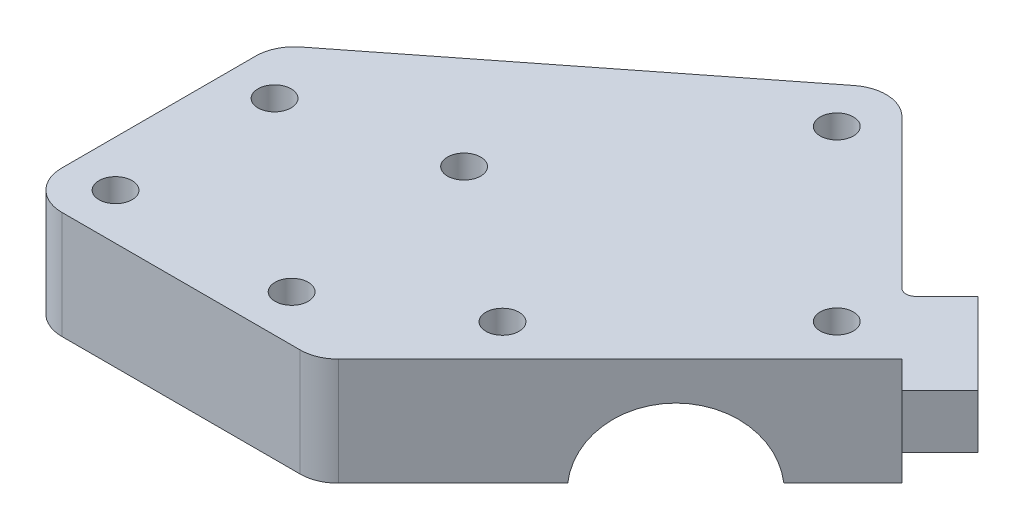
SolidWorks part; units mm, degrees
ref_plane "前视基准面" through (0, 0, 0) normal (0, 0, 1) x (1, 0, 0)
ref_plane "上视基准面" through (0, 0, 0) normal (0, 1, 0) x (1, 0, 0)
ref_plane "右视基准面" through (0, 0, 0) normal (1, 0, 0) x (0, 0, -1)
ref_plane "基准面4" through (0, 1, 0) normal (0, -1, 0) x (1, 0, 0)
sketch "草图1" plane through (0, 1, 0) normal (0, -1, 0) x (1, 0, 0)
  line L0 (4.7435, -52.275) -> (35.2198, -21.7987)
  line L1 (35.2198, -21.7987) -> (-2.9289, 16.35)
  line L2 (-2.9289, 16.35) -> (-41.0289, 16.35)
  line L3 (-41.0289, 16.35) -> (-41.0289, -16.35)
  line L4 (-41.0289, -16.35) -> (4.7435, -52.275)
extrude "凸台-拉伸1" add sketch "草图1" against normal blind 14
ref_plane "基准面5" through (0, 15, 0) normal (0, 1, 0) x (1, 0, 0)
sketch "草图2" plane through (0, 15, 0) normal (0, 1, 0) x (1, 0, 0)
  line L0 (35.2198, 21.7987) -> (38.7553, 18.2632)
  line L1 (38.7553, 18.2632) -> (43.705, 23.2129)
  line L2 (43.705, 23.2129) -> (33.0984, 33.8195)
  line L3 (33.0984, 33.8195) -> (28.1487, 28.8698)
  line L4 (28.1487, 28.8698) -> (35.2198, 21.7987)
extrude "凸台-拉伸2" add sketch "草图2" against normal blind 7
sketch "草图3" plane through (6.7105, 0, 6.7105) normal (0.7071, 0, 0.7071) x (0.7071, 0, -0.7071)
  line L0 (9.5383, 1) -> (29.4458, 1)
  arc A0 (29.4458, 1) -> (9.5383, 1) centre (19.492, 0.0398) ccw
extrude "切除-拉伸1" cut sketch "草图3" against normal blind 38.1
sketch "草图4" plane through (-41.0289, 0, 0) normal (-1, 0, 0) x (0, 0, 1)
  line L0 (-6.2708, 1) -> (5.5795, 1)
  arc A0 (5.5795, 1) -> (-6.2708, 1) centre (-0.3456, 0.0551) ccw
extrude "切除-拉伸2" cut sketch "草图4" against normal blind 41.0289
ref_plane "基准面6" through (0, 12, 0) normal (0, 1, 0) x (1, 0, 0)
ref_plane "基准面7" through (0, 17, 0) normal (0, -1, 0) x (1, 0, 0)
hole_wizard "M4 间隙孔1" positions "草图15" profile "草图14" hole size "M4" standard "ANSI Metric"
sketch "草图15" plane through (0, 15, 0) normal (0, 1, 0) x (1, 0, 0)
  point P0 (-35.0289, -10.35)
  point P1 (5, 0)
  point P2 (-15, 15)
  point P3 (-12.103, -10.35)
  point P4 (-35.0289, 10.35)
  point P5 (4.7435, 43.7897)
  point P6 (26.7345, 21.7987)
sketch "草图14" plane through (-35.0289, 15, 10.35) normal (1, 0, 0) x (0, 0, 1)
  line L0 (0, 0) -> (0, 14)
  line L1 (0, 14) -> (2.159, 14)
  line L2 (2.159, 14) -> (2.159, 0)
  line L5 (2.159, 0) -> (0, 0)
  line L11 (0, -6.35) -> (0, 107.95) construction
  dimension "通孔孔直径" = 4.318
  dimension "通孔孔深度" = 14
fillet "圆角1" radius 5 4 edges at (-2.9289, 8, 16.35) (-41.0289, 8, 16.35) (-41.0289, 8, -16.35) (4.7435, 8, -52.275)
fillet "圆角3" radius 1.27 1 edges at (28.1487, 11.5, -28.8698)
fillet "圆角4" radius 1.27 1 edges at (31.2352, 8, -25.7832)
